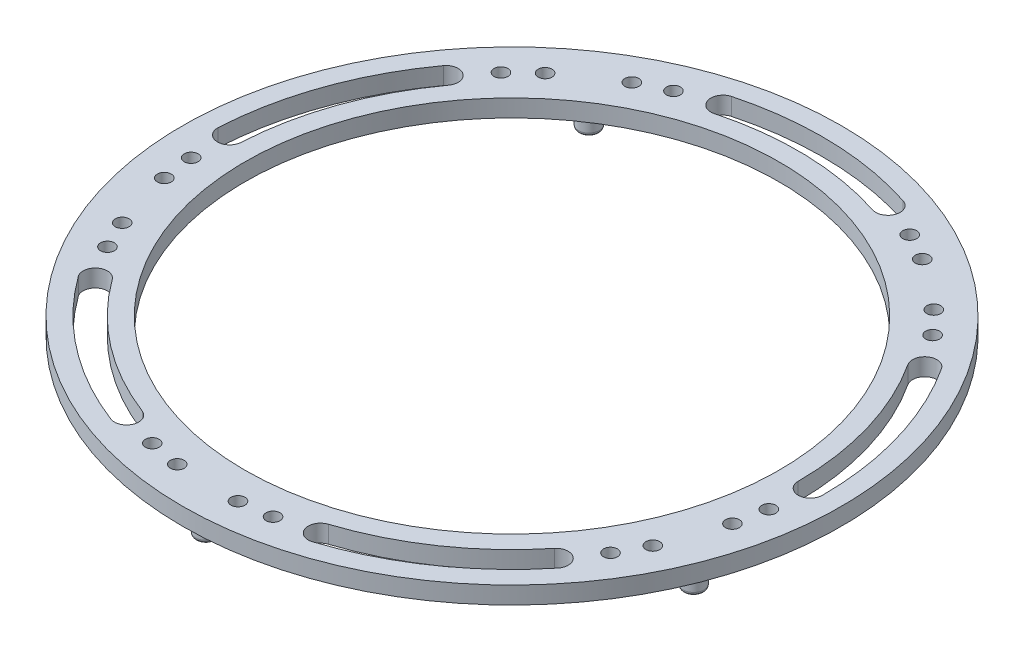
SolidWorks part; units mm, degrees
ref_plane "Front Plane" through (0, 0, 0) normal (0, 0, 1) x (1, 0, 0)
ref_plane "Top Plane" through (0, 0, 0) normal (0, 1, 0) x (1, 0, 0)
ref_plane "Right Plane" through (0, 0, 0) normal (1, 0, 0) x (0, 0, -1)
sketch "Sketch1" plane through (0, 0, 0) normal (0, 1, 0) x (1, 0, 0)
  circle A0 centre (0, 0) radius 47.5
  circle A1 centre (0, 0) radius 38.5
  dimension "D1" = 95
  dimension "D2" = 77
extrude "Boss-Extrude1" add sketch "Sketch1" along normal blind 2.5
sketch "Sketch2" plane through (0, 2.5, 0) normal (0, 1, 0) x (1, 0, 0)
  line L0 (-51.1462, 0) -> (67.8311, 0) construction
  line L1 (0, 54.0778) -> (0, -57.4459) construction
  line L2 (0, 0) -> (36.0628, 23.4195) construction
  line L3 (0, 0) -> (43, 0) construction
  line L4 (0, 0) -> (26.1767, 34.1142) construction
  arc A0 (36.0628, 23.4195) -> (43, 0) centre (0, 0) cw construction
  arc A1 (44.75, 0) -> (37.5305, 24.3726) centre (0, 0) ccw
  arc A2 (41.25, 0) -> (34.5952, 22.4664) centre (0, 0) ccw
  arc A3 (41.25, 0) -> (44.75, 0) centre (43, 0) ccw
  arc A4 (37.5305, 24.3726) -> (34.5952, 22.4664) centre (36.0628, 23.4195) ccw
  circle A5 centre (0, 0) radius 43 construction
  circle A6 centre (26.1767, 34.1142) radius 1.5
  point P8 (41.2292, 12.2127)
  dimension "D1" = 43
  dimension "D2" = 1.75
  dimension "D3" = 33
  dimension "D4" = 3
  dimension "D5" = 19.5
extrude "Cut-Extrude1" cut sketch "Sketch2" against normal up to next (2.5 mm away)
sketch "Sketch3" plane through (0, 2.5, 0) normal (0, 1, 0) x (1, 0, 0)
  circle A0 centre (26.1767, 34.1142) radius 1.5 construction
  circle A1 centre (26.1767, 34.1142) radius 1.5
  dimension "D1" = 3
extrude "Boss-Extrude2" add sketch "Sketch3" against normal blind 6.5
fillet "Fillet1" radius 0.5 2 edges at (26.1767, 0, -32.6142) (26.1767, -4, -32.6142)
pattern_circular "CirPattern1" count 5 over 360 about axis through (0, 0, 0) along (0, 1, 0) of "Cut-Extrude1", "Boss-Extrude2", "Fillet1"
sketch "Sketch4" plane through (0, 0, 0) normal (0, -1, 0) x (1, 0, 0)
  line L0 (0, 53.8912) -> (0, -53.2334) construction
  line L1 (-66.0167, 0) -> (73.1583, 0) construction
  line L2 (0, 0) -> (-1.1256, 42.9853) construction
  line L3 (0, 0) -> (-5.6126, 42.6321) construction
  line L4 (0, 0) -> (3.3737, 42.8674) construction
  line L5 (0, 0) -> (-10.0382, 41.8119) construction
  line L6 (0, 0) -> (7.8361, 42.28) construction
  circle A1 centre (0, 0) radius 43 construction
  circle A2 centre (-1.1256, 42.9853) radius 1 construction
  circle A3 centre (-1.1256, 42.9853) radius 1 construction
  circle A4 centre (-5.6126, 42.6321) radius 1
  circle A5 centre (3.3737, 42.8674) radius 1
  circle A6 centre (-10.0382, 41.8119) radius 1
  circle A7 centre (7.8361, 42.28) radius 1
  dimension "D1" = 86
  dimension "D2" = 2
  dimension "D3" = 2
  dimension "D6" = 2
  dimension "D8" = 2
  dimension "D4" = 6
  dimension "D5" = 6
  dimension "D7" = 6
  dimension "D9" = 6
extrude "Cut-Extrude2" cut sketch "Sketch4" against normal up to next (2.5 mm away)
pattern_circular "CirPattern2" count 5 over 360 about axis through (0, 0, 0) along (0, 1, 0) of "Cut-Extrude2"
